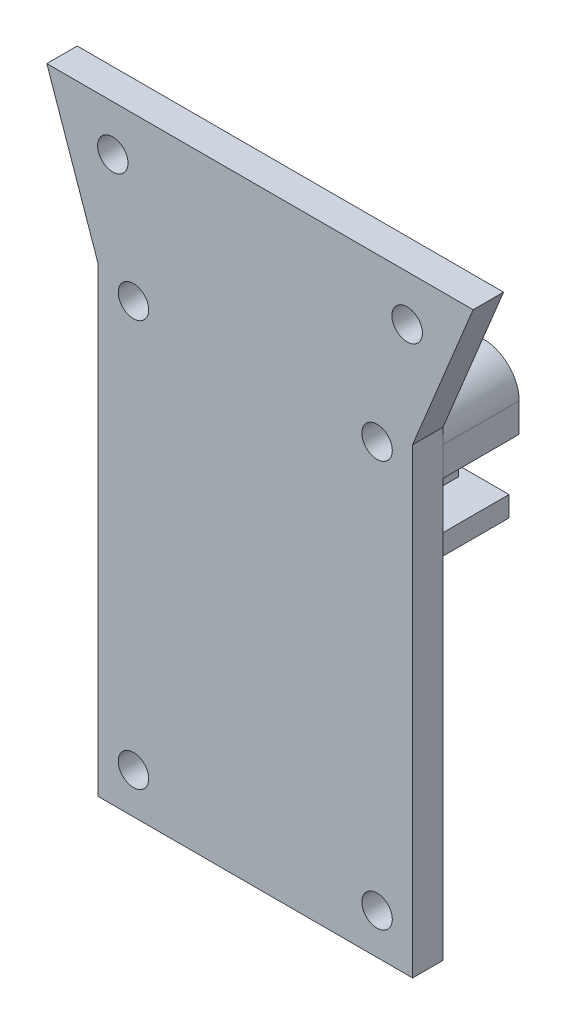
SolidWorks part; units mm, degrees
other "Markup1"
sketch "Sketch10" plane through (36.963, 0, 3) normal (0.1421, -0.5407, 0.8291) x (-0.9838, -0.1695, 0.058)
sketch "Sketch14" plane through (36.963, 0, 3) normal (0.1421, -0.5407, 0.8291) x (-0.9838, -0.1695, 0.058)
sketch "Sketch23" plane through (36.963, 0, 3) normal (0.1421, -0.5407, 0.8291) x (-0.9838, -0.1695, 0.058)
ref_plane "Front Plane" through (0, 0, 0) normal (0, 0, 1) x (1, 0, 0)
ref_plane "Top Plane" through (0, 0, 0) normal (0, 1, 0) x (1, 0, 0)
ref_plane "Right Plane" through (0, 0, 0) normal (1, 0, 0) x (0, 0, -1)
sketch "Sketch1" plane through (0, 0, 0) normal (0, 0, 1) x (1, 0, 0)
  line L1 (0, 0) -> (31, 0)
  line L2 (0, 0) -> (0, 45.5)
  line L3 (-5.037, 60) -> (36.963, 60)
  line L4 (31, 0) -> (31, 45.5)
  line L5 (36.963, 60) -> (31, 45.5)
  line L7 (-5.037, 60) -> (0, 45.5)
  circle A0 centre (30.463, 55.5) radius 1.5
  circle A1 centre (27.5, 44) radius 1.5
  circle A4 centre (27.5, 4) radius 1.5
  circle A5 centre (3.5, 4) radius 1.5
  circle A7 centre (3.5, 44) radius 1.5
  circle A9 centre (1.463, 55.5) radius 1.5
  point P29 (15.963, 60)
  dimension "D4" = 3
  dimension "D5" = 21
  dimension "D6" = 2
  dimension "D7" = 2
  dimension "D8" = 21
  dimension "D9" = 2.5
  dimension "D10" = 37
  dimension "D11" = 2.8
  dimension "D12" = 29
  dimension "D13" = 14.5
  dimension "D14" = 11.5
  dimension "D15" = 3
  dimension "D16" = 5
  dimension "D2" = 0
  dimension "D3" = 31
extrude "Boss-Extrude1" add sketch "Sketch1" along normal blind 3
sketch "Sketch2" plane through (0, 0, 0) normal (0, 0, -1) x (-1, 0, 0)
  line L1 (0, 44) -> (0, 24.5)
  line L3 (0, 45.5) -> (0, 0) construction
  line L4 (0, 24.5) -> (-18, 24.5)
  line L8 (-31, 44) -> (-31, 41.136)
  line L9 (-31, 0) -> (-31, 45.5) construction
  line L11 (-18, 24.5) -> (-18, 28.5)
  line L12 (-18, 28.5) -> (-25, 28.5)
  line L14 (-24.0359, 43.5) -> (-6.9641, 43.5)
  line L16 (-25, 28.5) -> (-25, 35.136)
  line L17 (-25, 35.136) -> (-31, 41.136)
  circle A0 centre (-3.5, 44) radius 1.5 construction
  circle A1 centre (-27.5, 44) radius 1.5 construction
  circle A2 centre (-3.5, 44) radius 1.5 construction
  circle A3 centre (-27.5, 44) radius 1.5 construction
  circle A4 centre (-27.5, 44) radius 2.5
  circle A5 centre (-3.5, 44) radius 2.5
  arc A6 (0, 44) -> (-6.9641, 43.5) centre (-3.5, 44) ccw
  arc A7 (-24.0359, 43.5) -> (-31, 44) centre (-27.5, 44) ccw
  dimension "D1" = 5
  dimension "D2" = 7
  dimension "D3" = 5
  dimension "D4" = 7
  dimension "D6" = 18
  dimension "D9" = 2
  dimension "D10" = 45
  dimension "D11" = 2
  dimension "D8" = 15
  dimension "D5" = 19
  dimension "D7" = 25
extrude "Boss-Extrude2" add sketch "Sketch2" along normal blind 1.5 separate body contours L8 A7
sketch "Sketch5" plane through (0, 0, -1.5) normal (0, 0, -1) x (-1, 0, 0)
  line L0 (-23, 41.5) -> (-5.5, 41.5)
  line L1 (-5.5, 42.5) -> (-5.5, 41.5)
  line L2 (-6.9641, 43.5) -> (-24.0359, 43.5) construction
  line L3 (-2, 42) -> (-2, 26.5)
  line L4 (-2, 26.5) -> (-16, 26.5)
  line L5 (-16, 26.5) -> (-16, 30.5)
  line L6 (-16, 30.5) -> (-23, 30.5)
  line L7 (-23, 30.5) -> (-23, 41.5)
  line L11 (-6.9641, 43.5) -> (-24.0359, 43.5)
  line L12 (-31, 44) -> (-31, 41.136)
  line L13 (-31, 41.136) -> (-25, 35.136)
  line L14 (-25, 35.136) -> (-25, 28.5)
  line L15 (-25, 28.5) -> (-18, 28.5)
  line L16 (-18, 28.5) -> (-18, 24.5)
  line L17 (-18, 24.5) -> (0, 24.5)
  line L18 (0, 24.5) -> (0, 44)
  line L19 (-6.9641, 43.5) -> (-24.0359, 43.5)
  line L20 (-31, 44) -> (-31, 41.136)
  line L21 (-31, 41.136) -> (-25, 35.136)
  line L22 (-25, 35.136) -> (-25, 28.5)
  line L23 (-25, 28.5) -> (-18, 28.5)
  line L24 (-18, 28.5) -> (-18, 24.5)
  line L25 (-18, 24.5) -> (0, 24.5)
  line L26 (0, 24.5) -> (0, 44)
  circle A0 centre (-3.5, 44) radius 2.5 construction
  circle A1 centre (-27.5, 44) radius 2.5 construction
  arc A2 (-2, 42) -> (-5.5, 42.5) centre (-3.5, 44) ccw
  arc A3 (0, 44) -> (-6.9641, 43.5) centre (-3.5, 44) ccw
  arc A4 (-24.0359, 43.5) -> (-31, 44) centre (-27.5, 44) ccw
  arc A5 (0, 44) -> (-6.9641, 43.5) centre (-3.5, 44) ccw
  arc A6 (-24.0359, 43.5) -> (-31, 44) centre (-27.5, 44) ccw
  circle A7 centre (-27.5, 44) radius 2.5
  dimension "D1" = 2
  dimension "D3" = 2
  dimension "D4" = 2
  dimension "D5" = 2
  dimension "D6" = 2
  dimension "D7" = 2
  dimension "D8" = 2
  dimension "D2" = 0
extrude "Boss-Extrude5" add sketch "Sketch5" along normal blind 6
sketch "Sketch9" plane through (0, 24.5, 0) normal (0, -1, 0) x (1, 0, 0)
  line L0 (10, 0) -> (10, -8)
  line L1 (23.1, 0) -> (-23.1, 0) construction
  line L2 (10, -8) -> (22, -8)
  line L3 (22, -8) -> (22, 0)
  line L4 (22, 0) -> (10, 0)
  line L5 (0, -7.5) -> (0, 0) construction
  dimension "D1" = 10
  dimension "D2" = 8
  dimension "D3" = 12
extrude "Cut-Extrude2" cut sketch "Sketch9" against normal blind 6 contours L0 L2 L3 L4
sketch "Sketch11" plane through (25, 0, 0) normal (1, 0, 0) x (0, 0, -1)
  line L0 (4, 30.5) -> (4, 34.5)
  line L2 (4, 34.5) -> (12, 34.5)
  line L3 (12, 34.5) -> (12, 30.5)
  line L4 (12, 30.5) -> (4, 30.5)
  line L5 (0, 35.136) -> (0, 28.5) construction
  line L6 (7.5, 28.5) -> (0, 28.5) construction
  dimension "D1" = 4
  dimension "D2" = 4
  dimension "D3" = 8
  dimension "D4" = 2
extrude "Cut-Extrude4" cut sketch "Sketch11" against normal blind 2 contours L2 L3 L4 L0
sketch "Sketch13" plane through (0, 0, 0) normal (0, 0, 1) x (1, 0, 0)
  line L0 (13, 43.5) -> (13, 30.5)
  line L1 (6.9641, 43.5) -> (24.0359, 43.5) construction
  line L2 (22, 30.5) -> (10, 30.5) construction
  line L3 (13, 30.5) -> (18, 30.5)
  line L4 (18, 30.5) -> (18, 43.5)
  line L5 (18, 43.5) -> (13, 43.5)
  line L6 (6.9641, 43.5) -> (24.0359, 43.5) construction
  point P6 (15.5, 43.5)
  point P9 (15.5, 43.5)
  dimension "D1" = 5
extrude "Cut-Extrude7" cut sketch "Sketch13" against normal up to surface (1.5 mm away) up to face at (11.456, 34.5861, -1.5)
sketch "Sketch16" plane through (-5.068, 5.068, 0) normal (0.7071, -0.7071, 0) x (0, 0, -1)
  line L0 (7.5, 45.6084) -> (1.5, 45.6084) construction
  line L1 (7.5, 45.6084) -> (1.5, 45.6084) construction
  line L2 (0, 53.0581) -> (0, 48.0581) construction
  line L3 (0, 53.0581) -> (0, 48.0581) construction
  line L4 (0, 51.0079) -> (0, 42.5226)
  line L5 (0, 42.5226) -> (7.5, 42.5226)
  line L7 (7.5, 51.0079) -> (0, 51.0079)
  line L8 (0, 51.0079) -> (0, 48.0581) construction
  line L12 (7.5, 45.6084) -> (1.5, 45.6084) construction
  line L13 (0, 48.0581) -> (17.5, 48.0581) construction
  line L14 (5.5, 48.6084) -> (5.5, 46.6084)
  line L16 (7.5, 46.6084) -> (7.5, 48.6084)
  line L17 (7.5, 48.6084) -> (5.5, 48.6084)
  line L18 (7.5, 51.0079) -> (7.5, 42.5226) construction
  line L21 (12, 40.6586) -> (12, 42.0729) construction
  line L22 (5.5, 46.6084) -> (7.5, 46.6084)
  line L27 (7.5, 42.5226) -> (7.5, 51.0079)
  line L28 (7.5, 42.5226) -> (7.5, 51.0079)
  point P17 (7.5, 48.6084)
  dimension "D2" = 2
  dimension "D4" = 4.5
  dimension "D5" = 2
  dimension "D6" = 1
  dimension "D1" = 0
extrude "Cut-Extrude9" cut sketch "Sketch16" against normal through all contours L14 L22 L16 L17
sketch "Sketch19" plane through (0, 0, -7.5) normal (0, 0, -1) x (-1, 0, 0)
  line L2 (-18, 28.5) -> (-25, 28.5)
  line L3 (-25, 28.5) -> (-25, 30.5)
  line L12 (-25, 30.5) -> (-16, 30.5)
  line L13 (-16, 26.5) -> (0, 26.5)
  line L14 (0, 24.5) -> (0, 44) construction
  line L15 (-5.5, 41.5) -> (-23, 41.5)
  line L16 (-31, 44) -> (-31, 41.136)
  line L17 (-31, 41.136) -> (-25, 35.136)
  line L18 (-25, 35.136) -> (-25, 28.5)
  line L19 (-25, 28.5) -> (-18, 28.5)
  line L20 (-18, 28.5) -> (-18, 24.5)
  line L21 (-18, 24.5) -> (0, 24.5)
  line L22 (0, 24.5) -> (0, 44)
  line L23 (-6.9641, 43.5) -> (-24.0359, 43.5)
  line L28 (-18, 28.5) -> (-18, 24.5)
  line L32 (-5.5, 42.5) -> (-5.5, 41.5)
  line L33 (-2, 26.5) -> (-2, 42)
  line L34 (-16, 26.5) -> (-2, 26.5)
  line L35 (-16, 30.5) -> (-16, 26.5)
  line L36 (-23, 30.5) -> (-16, 30.5)
  line L37 (-23, 41.5) -> (-23, 30.5)
  line L42 (-16, 30.5) -> (-16, 26.5)
  line L44 (0, 26.5) -> (0, 24.5)
  line L45 (0, 24.5) -> (-18, 24.5)
  arc A3 (-2, 42) -> (-5.5, 42.5) centre (-3.5, 44) ccw
  arc A4 (0, 44) -> (-6.9641, 43.5) centre (-3.5, 44) ccw
  arc A5 (-24.0359, 43.5) -> (-31, 44) centre (-27.5, 44) ccw
  dimension "D3" = 0
  dimension "D4" = 0
extrude "Boss-Extrude6" add sketch "Sketch19" along normal blind 5
sketch "Sketch20" plane through (0, 0, 0) normal (-1, 0, 0) x (0, 0, 1)
  line L0 (-4, 26.5) -> (-7.5, 26.5)
  line L1 (-7.5, 26.5) -> (-7.5, 34.5)
  line L2 (-7.5, 34.5) -> (-4, 34.5)
  line L3 (-4, 34.5) -> (-4, 26.5)
  line L4 (0, -23.1) -> (0, 23.1) construction
  line L5 (-12.5, 24.5) -> (0, 24.5) construction
  line L7 (-7.5, 26.5) -> (-7.5, 44) construction
  dimension "D1" = 4
  dimension "D2" = 2
  dimension "D3" = 8
extrude "Cut-Extrude10" cut sketch "Sketch20" against normal blind 2
sketch "Sketch21" plane through (0, 28.5, 0) normal (0, -1, 0) x (1, 0, 0)
  line L0 (22, -5) -> (19.5, -7.5)
  line L1 (22, 0) -> (22, -7.5) construction
  line L2 (5.5, -7.5) -> (23, -7.5) construction
  line L3 (19.5, -7.5) -> (22, -7.5)
  line L4 (22, -7.5) -> (22, -5)
  line L5 (23.1, 0) -> (-23.1, 0) construction
  dimension "D1" = 5
  dimension "D2" = 45
extrude "Boss-Extrude7" add sketch "Sketch21" against normal blind 2
sketch "Sketch22" plane through (0, 24.5, 0) normal (0, -1, 0) x (1, 0, 0)
  line L5 (13, -1.5) -> (10, -1.5) construction
  line L6 (0, -12.5) -> (0, 0) construction
  circle A0 centre (8, -7.5) radius 6
  dimension "D1" = 6
  dimension "D2" = 12
  dimension "D3" = 8
